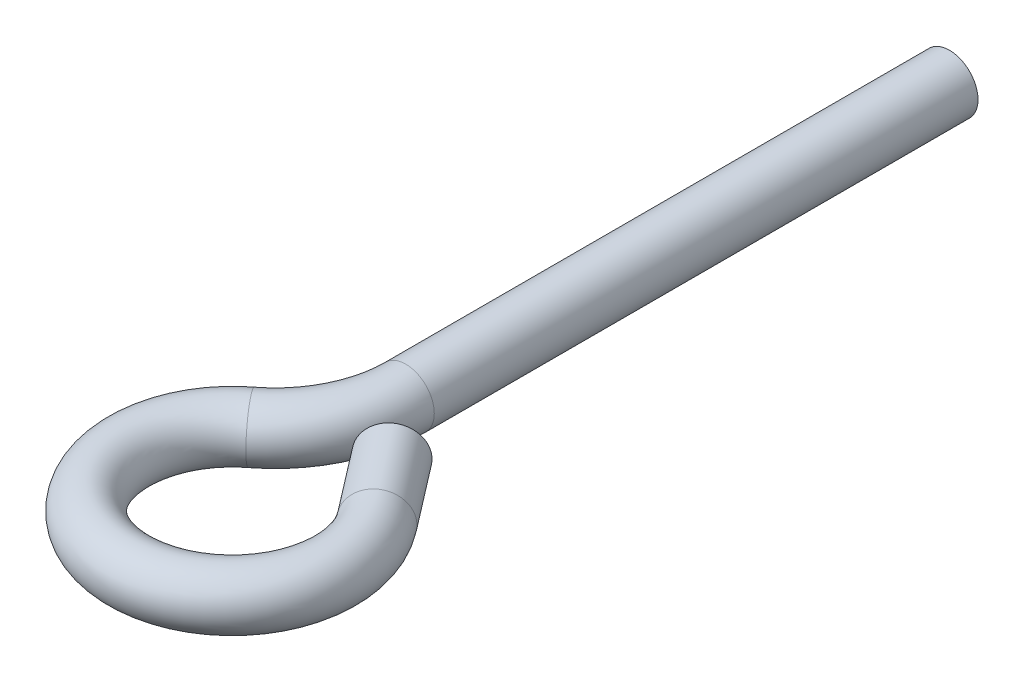
SolidWorks part; units mm, degrees
ref_plane "Front Plane" through (0, 0, 0) normal (0, 0, 1) x (1, 0, 0)
ref_plane "Top Plane" through (0, 0, 0) normal (0, 1, 0) x (1, 0, 0)
ref_plane "Right Plane" through (0, 0, 0) normal (1, 0, 0) x (0, 0, -1)
sketch "Sketch1" plane through (0, 0, 0) normal (0, 0, 1) x (1, 0, 0)
  circle A0 centre (0, 0) radius 2.667
  dimension "D1" = 5.334
extrude "Boss-Extrude1" add sketch "Sketch1" along normal blind 50.8
sketch "Sketch2" plane through (0, 0, 50.8) normal (0, 0, 1) x (1, 0, 0)
  line L0 (0, 0) -> (-2.667, 0)
  line L1 (-2.667, 0) -> (-12.192, 0)
  line L2 (-12.192, -2.667) -> (-12.192, 2.667)
  circle A0 centre (0, 0) radius 2.667
  point P7 (-12.192, 0)
  dimension "D1" = 9.525
revolve "Revolve1" add sketch "Sketch2" angle 52.5 about L2
sketch "Sketch3" plane through (-32.2083, 0, 24.7143) normal (-0.7934, 0, 0.6088) x (0.6088, 0, 0.7934)
  line L0 (50.0901, 0) -> (47.7393, 0)
  line L1 (47.7393, 0) -> (54.7243, 0)
  line L2 (54.7243, -2.667) -> (54.7243, 2.667)
  circle A0 centre (50.0901, 0) radius 2.3508
  circle A1 centre (45.0723, 0) radius 2.667 construction
  point P2 (50.0901, 0)
  point P8 (54.7243, 0)
  point P9 (52.7571, 0)
  dimension "D1" = 6.985
revolve "Revolve2" add sketch "Sketch3" angle 270 about L2
sketch "Sketch4" plane through (33.3141, 0, 43.4157) normal (-0.6088, 0, -0.7934) x (-0.7934, 0, 0.6088)
  circle A0 centre (30.9456, 0) radius 2.667
extrude "Boss-Extrude2" add sketch "Sketch4" along normal blind 7.62
sketch "Sketch5" plane through (28.6753, 0, 37.3704) normal (-0.6088, 0, -0.7934) x (-0.7934, 0, 0.6088)
  circle A0 centre (30.9456, 0) radius 2.667 construction
  point P0 (30.9456, 2.667)
ref_plane "Plane1" through (8.7632, 2.667, 62.2542) normal (0, 1, 0) x (1, 0, 0)
